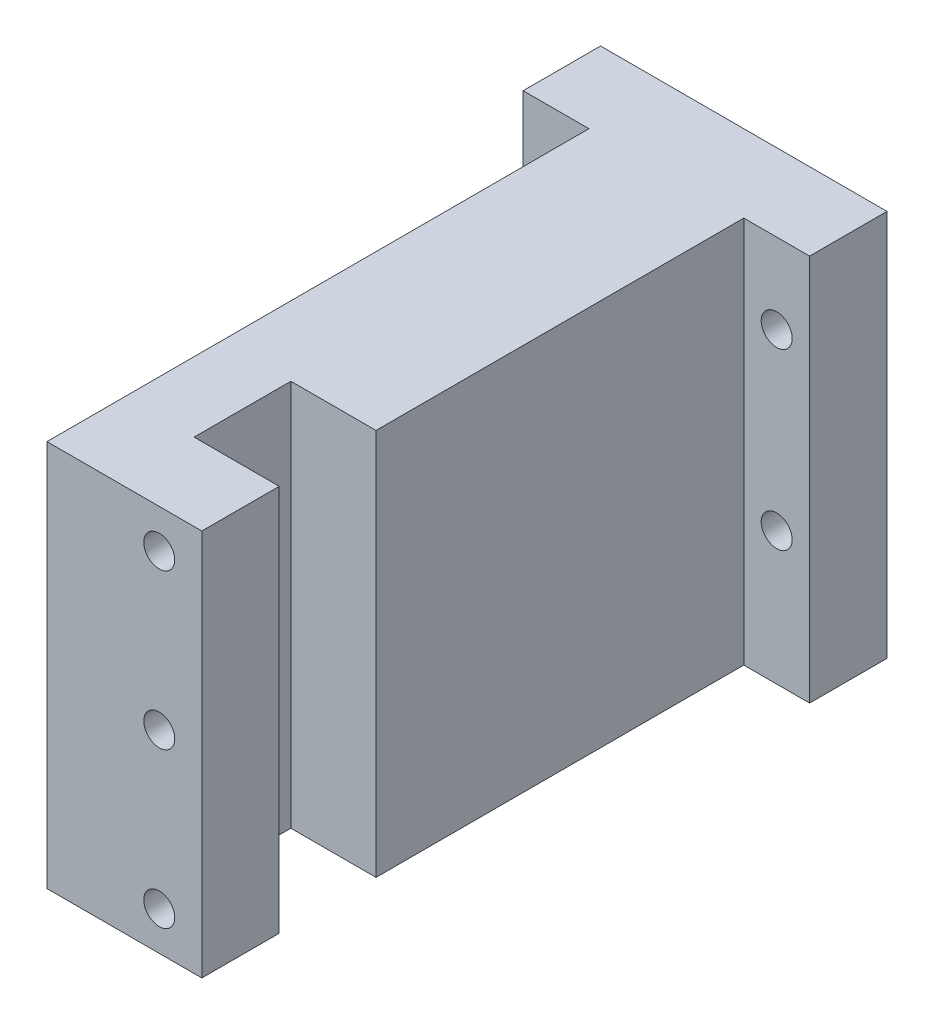
SolidWorks part; units mm, degrees
ref_plane "Płaszczyzna przednia" through (0, 0, 0) normal (0, 0, 1) x (1, 0, 0)
ref_plane "Płaszczyzna górna" through (0, 0, 0) normal (0, 1, 0) x (1, 0, 0)
ref_plane "Płaszczyzna prawa" through (0, 0, 0) normal (1, 0, 0) x (0, 0, -1)
sketch "Szkic1" plane through (0, 0, 0) normal (0, 0, 1) x (1, 0, 0)
  line L0 (-37, -50) -> (37, 50) construction
  line L1 (-37, 50) -> (37, 50)
  line L2 (-37, 50) -> (-37, -50)
  line L3 (-37, -50) -> (37, -50)
  line L4 (37, 50) -> (37, -50)
  line L5 (37, -50) -> (-37, 50) construction
  point P0 (0, 0)
  point P5 (0, 0)
  point P6 (0, 0)
  dimension "D1" = 74
  dimension "D2" = 100
extrude "Dodanie-wyciągnięcie1" add sketch "Szkic1" along normal blind 20
sketch "Szkic3" plane through (0, 0, 20) normal (0, 0, 1) x (1, 0, 0)
  line L0 (-37, 50) -> (-37, -50) construction
  line L4 (-20, 50) -> (-20, -50)
  line L5 (20, -50) -> (-20, -50)
  line L7 (20, -50) -> (20, 50)
  line L8 (20, 50) -> (-20, 50)
  line L10 (-37, -50) -> (37, -50) construction
  line L11 (-20, -50) -> (-20, 50)
  line L15 (20, 50) -> (20, -50)
  line L16 (37, 50) -> (-37, 50) construction
  line M4 (37, 50) -> (-37, 50)
  line M6 (-37, -50) -> (37, -50)
  dimension "D1" = 17
  dimension "D2" = 40
extrude "Dodanie-wyciągnięcie2" add sketch "Szkic3" along normal blind 140 contours L7 L4 M6 M4
sketch "Szkic4" plane through (0, 0, 20) normal (0, 0, 1) x (1, 0, 0)
  line L0 (-37, 50) -> (-37, -50) construction
  line L1 (-20, 50) -> (-37, 50) construction
  circle A0 centre (-28.5, 29.3) radius 4
  dimension "D1" = 8.5
  dimension "D2" = 20.7
extrude "Wytnij-wyciągnięcie1" cut sketch "Szkic4" against normal blind 20
pattern_linear "Szyk liniowy1" count 2 spacing 45 along (0, -1, 0) count 2 spacing 57 along (1, 0, 0) of "Wytnij-wyciągnięcie1"
sketch "Szkic5" plane through (0, 50, 0) normal (0, 1, 0) x (1, 0, 0)
  line L1 (-2, -140) -> (20, -140)
  line L2 (-2, -140) -> (-2, -115)
  line L3 (-2, -115) -> (20, -115)
  line L4 (20, -140) -> (20, -115)
  line L5 (20, -160) -> (-20, -160) construction
  line L6 (20, -160) -> (20, -20) construction
  dimension "D1" = 22
  dimension "D2" = 20
  dimension "D3" = 25
extrude "Wytnij-wyciągnięcie2" cut sketch "Szkic5" against normal blind 100
sketch "Szkic6" plane through (0, 0, 160) normal (0, 0, 1) x (1, 0, 0)
  line L0 (-20, -50) -> (20, -50) construction
  line L2 (20, -50) -> (20, 50) construction
  circle A0 centre (9, 40) radius 4
  circle A1 centre (9, 0) radius 4
  circle A2 centre (9, -40) radius 4
  dimension "D1" = 40
  dimension "D2" = 40
  dimension "D3" = 10
  dimension "D4" = 11
extrude "Wytnij-wyciągnięcie3" cut sketch "Szkic6" against normal blind 10
